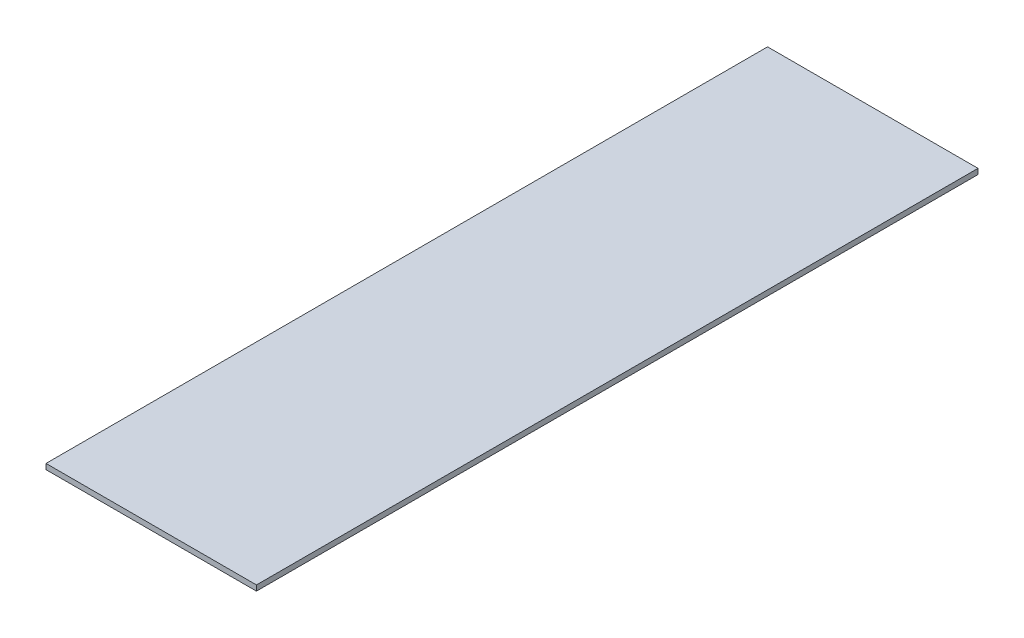
SolidWorks part; units mm, degrees
ref_plane "Front Plane" through (0, 0, 0) normal (0, 0, 1) x (1, 0, 0)
ref_plane "Top Plane" through (0, 0, 0) normal (0, 1, 0) x (1, 0, 0)
ref_plane "Right Plane" through (0, 0, 0) normal (1, 0, 0) x (0, 0, -1)
sketch "Sketch1" plane through (0, 0, 0) normal (0, 1, 0) x (1, 0, 0)
  line L1 (0, 0) -> (700, 0)
  line L2 (0, 0) -> (0, 2400)
  line L3 (0, 2400) -> (700, 2400)
  line L4 (700, 0) -> (700, 2400)
  dimension "D1" = 2400
  dimension "D2" = 700
extrude "Boss-Extrude1" add sketch "Sketch1" along normal blind 18
